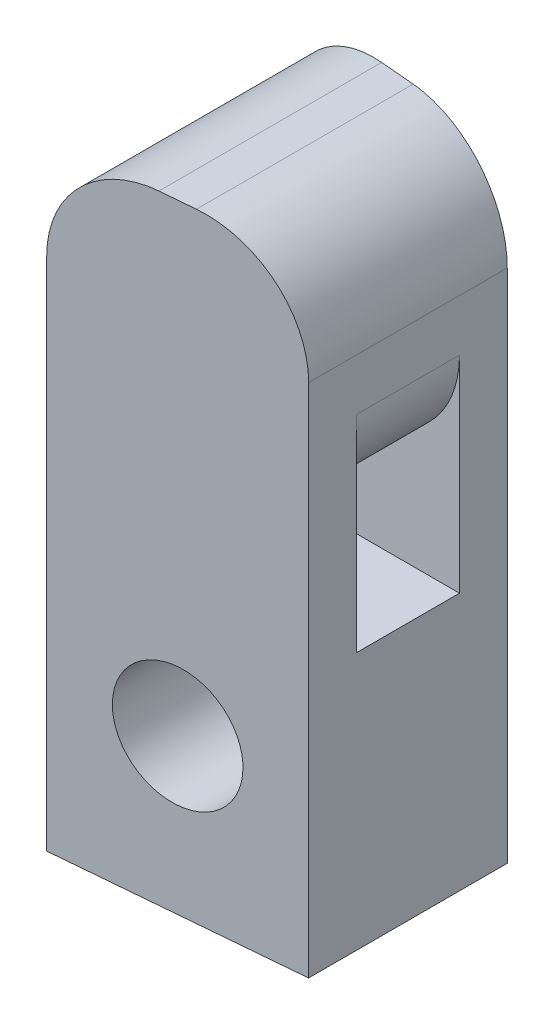
SolidWorks part; units mm, degrees
ref_plane "Front Plane" through (0, 0, 0) normal (0, 0, 1) x (1, 0, 0)
ref_plane "Top Plane" through (0, 0, 0) normal (0, 1, 0) x (1, 0, 0)
ref_plane "Right Plane" through (0, 0, 0) normal (1, 0, 0) x (0, 0, -1)
sketch "Sketch2" plane through (0, 0, 0) normal (0, 1, 0) x (1, 0, 0)
  line L0 (-2.335, -2.335) -> (2.335, -2.335) construction
  line L1 (-2.335, -2.335) -> (-2.335, 2.335)
  line L2 (2.335, -2.335) -> (2.335, 2.335) construction
  line L3 (-2.335, 2.335) -> (2.335, 2.335) construction
  line L4 (-2.335, -2.335) -> (2.335, 2.335) construction
  line L5 (2.335, -2.335) -> (-2.335, 2.335) construction
  line L6 (-2.335, 2.335) -> (2.335, 1.9264)
  line L7 (-2.335, -2.335) -> (2.335, -1.9264)
  line L8 (2.335, -1.9264) -> (2.335, 1.9264)
  point P1 (0, 0)
  dimension "D1" = 5
  dimension "D2" = 5
  dimension "D3" = 4.67
  dimension "D4" = 4.67
extrude "Boss-Extrude1" add sketch "Sketch2" along normal blind 10
sketch "Sketch3" plane through (0, 10, 0) normal (0, 1, 0) x (1, 0, 0)
  line L4 (2.335, -1.9264) -> (2.335, 1.9264)
  line L5 (2.335, 1.9264) -> (-2.335, 2.335)
  line L6 (-2.335, 2.335) -> (-2.335, -2.335)
  line L7 (-2.335, -2.335) -> (2.335, -1.9264)
  line L8 (2.335, -1.9264) -> (2.335, 1.9264)
  line L9 (2.335, 1.9264) -> (-2.335, 2.335)
  line L10 (-2.335, 2.335) -> (-2.335, -2.335)
  line L11 (-2.335, -2.335) -> (2.335, -1.9264)
  dimension "D1" = 0
extrude "Boss-Extrude2" add sketch "Sketch3" along normal blind 2
sketch "Sketch4" plane through (2.335, 0, 0) normal (1, 0, 0) x (0, 0, -1)
  line L0 (0, 0) -> (0, 12) construction
  line L1 (-1.9264, 12) -> (1.9264, 12) construction
  line L3 (-1, 5) -> (1, 5)
  line L4 (-1, 5) -> (-1, 7)
  line L5 (-1, 7) -> (1, 7)
  line L6 (1, 5) -> (1, 7)
  line L7 (-1, 5) -> (1, 7) construction
  line L8 (-1, 7) -> (1, 5) construction
  point P5 (0, 6)
  dimension "D1" = 2
  dimension "D2" = 2
extrude "Cut-Extrude1" cut sketch "Sketch4" against normal up to surface (4.67 mm away) up to face at (-2.335, 6, 0)
fillet "Fillet1" radius 2 4 edges at (2.335, 12, 0) (-2.335, 12, 0) (-2.335, 7, 0) (2.335, 7, 0)
sketch "Sketch6" plane through (0, 0, 0) normal (0, 0, 1) x (1, 0, 0)
  line L0 (0, 0) -> (0, 3) construction
  circle A0 centre (0, 3) radius 1.165
  dimension "D2" = 2.33
  dimension "D1" = 3
extrude "Cut-Extrude2" cut sketch "Sketch6" against normal through all both and the other way through all
equation "\"chuck_width\"=5"
equation "\"D3@Sketch2\"=\"chuck_width\"-\"tol\""
equation "\"chuck_length\"=5"
equation "\"D4@Sketch2\"=\"chuck_length\"-\"tol\""
equation "\"chuck_angle\"=5"
equation "\"D2@Sketch2\"=\"chuck_angle\""
equation "\"D1@Sketch2\"=\"chuck_angle\""
equation "\"chuck_depth\"=10"
equation "\"chuck_height\"= 2"
equation "\"pin_offset\"=3"
equation "\"D1@Sketch6\"=\"pin_offset\""
equation "\"pin_dia\"=2"
equation "\"D2@Sketch6\"=\"pin_dia\"+\"tol\""
equation "\"tol\"= 0.33"
